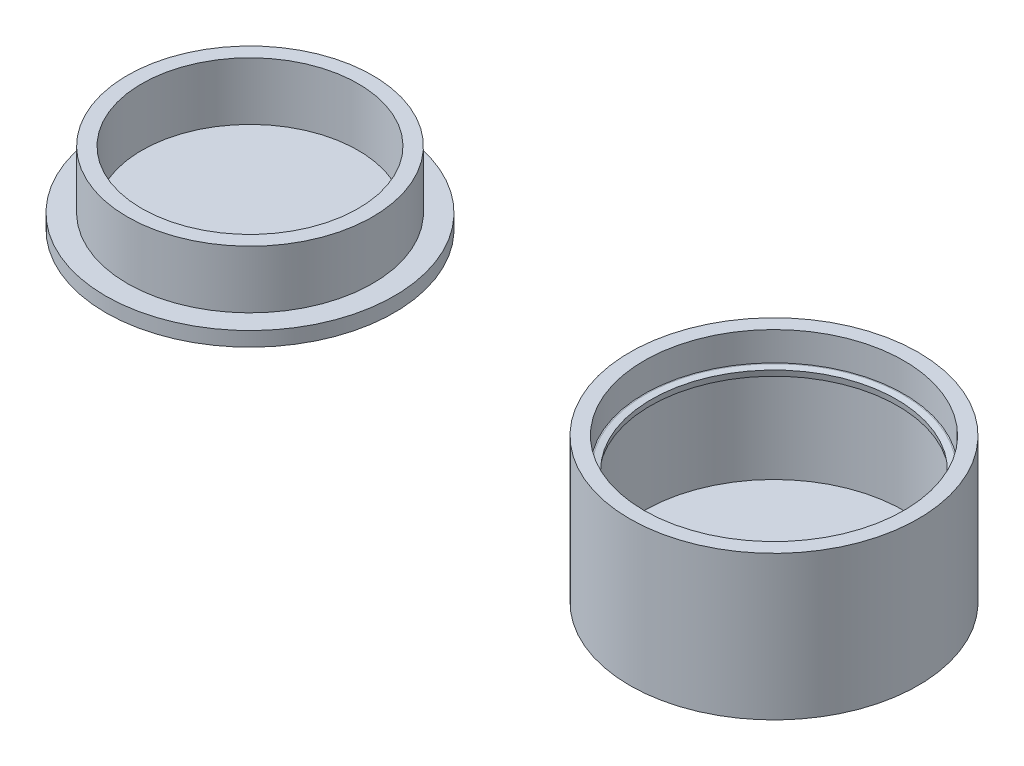
SolidWorks part; units mm, degrees
ref_plane "Front Plane" through (0, 0, 0) normal (0, 0, 1) x (1, 0, 0)
ref_plane "Top Plane" through (0, 0, 0) normal (0, 1, 0) x (1, 0, 0)
ref_plane "Right Plane" through (0, 0, 0) normal (1, 0, 0) x (0, 0, -1)
sketch "Sketch1" plane through (0, 0, 0) normal (0, 1, 0) x (1, 0, 0)
  circle A0 centre (0, 0) radius 20
extrude "Boss-Extrude2" add sketch "Sketch1" along normal blind 20 contours A0
sketch "Sketch2" plane through (0, 20, 0) normal (0, 1, 0) x (1, 0, 0)
  circle A0 centre (0, 0) radius 18
  circle A1 centre (0, 0) radius 20 construction
  dimension "D1" = 2
extrude "Cut-Extrude1" cut sketch "Sketch2" against normal blind 4
sketch "Sketch4" plane through (0, 16, 0) normal (0, 1, 0) x (1, 0, 0)
  circle A0 centre (0, 0) radius 17
extrude "Cut-Extrude2" cut sketch "Sketch4" against normal blind 1
sketch "Sketch5" plane through (0, 15, 0) normal (0, 1, 0) x (1, 0, 0)
  circle A0 centre (0, 0) radius 18
extrude "Cut-Extrude4" cut sketch "Sketch5" against normal blind 13
chamfer "Chamfer1" distance 0.85 angle 10 2 edges at (0, 16, 17) (0, 15, 17)
sketch "Sketch6" plane through (0, 0, 0) normal (0, 1, 0) x (1, 0, 0)
  circle A0 centre (-81.0658, 8.4286) radius 20
extrude "Boss-Extrude3" add sketch "Sketch6" along normal blind 2 separate body
sketch "Sketch8" plane through (0, 2, 0) normal (0, 1, 0) x (1, 0, 0)
  circle A0 centre (-81.0658, 8.4286) radius 17
  circle A1 centre (-81.0658, 8.4286) radius 20 construction
  circle A2 centre (-81.0658, 8.4286) radius 15
  dimension "D1" = 0
  dimension "D2" = 3
  dimension "D3" = 2
extrude "Boss-Extrude5" add sketch "Sketch8" along normal blind 8
